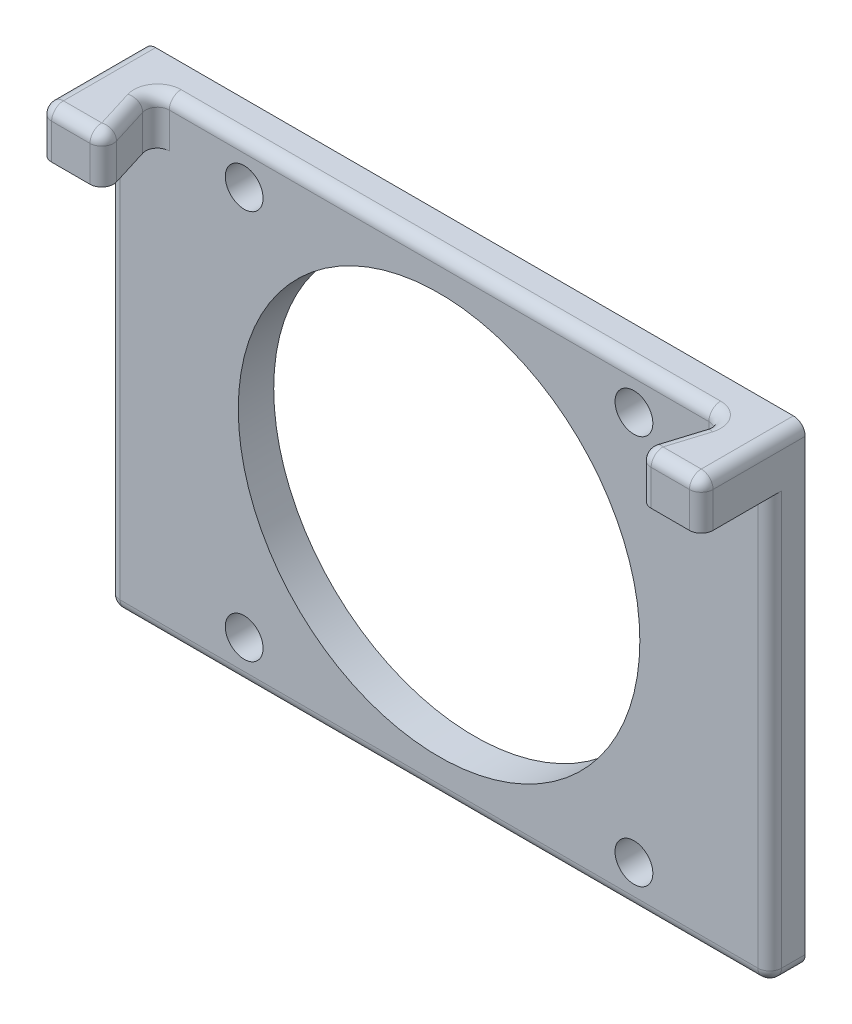
SolidWorks part; units mm, degrees
ref_plane "Plan de face" through (0, 0, 0) normal (0, 0, 1) x (1, 0, 0)
ref_plane "Plan de dessus" through (0, 0, 0) normal (0, 1, 0) x (1, 0, 0)
ref_plane "Plan de droite" through (0, 0, 0) normal (1, 0, 0) x (0, 0, -1)
sketch "Esquisse1" plane through (0, 0, 0) normal (0, 0, 1) x (1, 0, 0)
  line L1 (-28, 20) -> (28, 20)
  line L2 (-28, 20) -> (-28, -20)
  line L3 (-28, -20) -> (28, -20)
  line L4 (28, 20) -> (28, -20)
  dimension "D1" = 56
  dimension "D2" = 40
  dimension "D3" = 28
  dimension "D4" = 20
extrude "Boss.-Extru.1" add sketch "Esquisse1" along normal blind 3
sketch "Esquisse2" plane through (0, 0, 3) normal (0, 0, 1) x (1, 0, 0)
  line L1 (-28, 20) -> (-24.2, 20)
  line L2 (-28, 20) -> (-28, 16)
  line L3 (-28, 16) -> (-24.2, 16)
  line L4 (-24.2, 20) -> (-24.2, 16)
  line L5 (28, 20) -> (24.2, 20)
  line L6 (28, 20) -> (28, 16)
  line L7 (28, 16) -> (24.2, 16)
  line L8 (24.2, 20) -> (24.2, 16)
  dimension "D1" = 4
  dimension "D2" = 4
  dimension "D3" = 3.8
  dimension "D4" = 3.8
extrude "Boss.-Extru.2" add sketch "Esquisse2" along normal blind 5.8
sketch "Esquisse3" plane through (0, 20, 0) normal (0, 1, 0) x (1, 0, 0)
  line L0 (-24.2, -3) -> (-22.4, -8.8)
  line L1 (-22.4, -8.8) -> (-24.2, -8.8)
  line L2 (-24.2, -8.8) -> (-24.2, -3)
  line L3 (24.2, -3) -> (24.2, -8.8)
  line L4 (24.2, -8.8) -> (22.4, -8.8)
  line L5 (22.4, -8.8) -> (24.2, -3)
  dimension "D1" = 1.8
  dimension "D2" = 1.8
extrude "Boss.-Extru.3" add sketch "Esquisse3" against normal up to surface (4 mm away) up to face at (-26.575, 16, 6.625)
fillet "Congé1" radius 1 18 edges at (23.3, 20, 5.9) (28, -20, 1.5) (-28, -20, 1.5) (-28, 20, 4.4) (28, 20, 4.4) (25.2, 20, 8.8) (-25.2, 20, 8.8) (0, -20, 3) (28, -2, 3) (24.2, 18, 3) (22.4, 18, 8.8) (28, 18, 8.8) (-28, 18, 8.8) (-22.4, 18, 8.8)
sketch "Esquisse4" plane through (0, 0, 0) normal (0, 0, -1) x (-1, 0, 0)
  line L0 (-27, 20) -> (27, 20) construction
  line L1 (-20, 20) -> (20, 20)
  line L2 (-20, 20) -> (-20, -20)
  line L3 (-20, -20) -> (20, -20)
  line L4 (20, 20) -> (20, -20)
  line L5 (27, -20) -> (-27, -20) construction
  circle A0 centre (-16.5, 16.5) radius 1.6
  circle A1 centre (16.5, 16.5) radius 1.6
  circle A2 centre (16.5, -16.5) radius 1.6
  circle A3 centre (-16.5, -16.5) radius 1.6
  dimension "D3" = 3.2
  dimension "D4" = 3.2
  dimension "D5" = 3.2
  dimension "D6" = 3.2
  dimension "D1" = 40
  dimension "D2" = 20
  dimension "D7" = 3.5
  dimension "D8" = 3.5
  dimension "D9" = 3.5
  dimension "D10" = 3.5
  dimension "D11" = 3.5
  dimension "D12" = 3.5
  dimension "D13" = 3.5
  dimension "D14" = 3.5
extrude "Enlèv. mat.-Extru.1" cut sketch "Esquisse4" against normal through all contours A0 | A3 | A1 | A2
sketch "Esquisse5" plane through (0, 0, 0) normal (0, 0, -1) x (-1, 0, 0)
  circle A0 centre (0, 0) radius 17
  dimension "D1" = 34
extrude "Enlèv. mat.-Extru.2" cut sketch "Esquisse5" against normal through all
